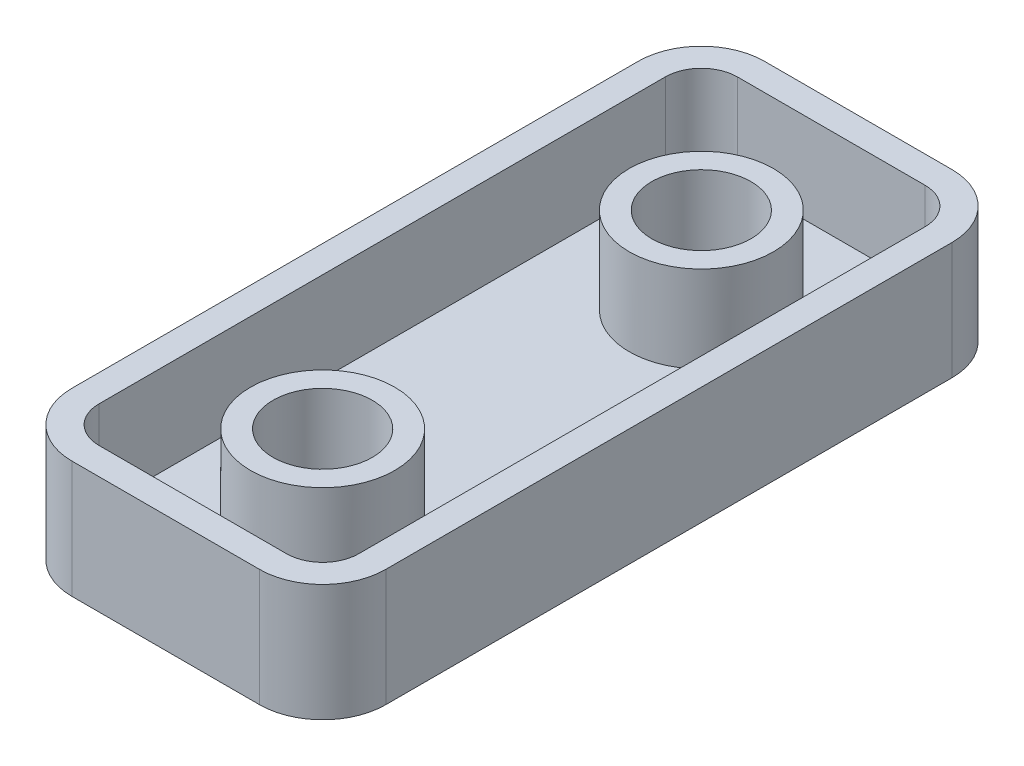
SolidWorks part; units mm, degrees
ref_plane "Front Plane" through (0, 0, 0) normal (0, 0, 1) x (1, 0, 0)
ref_plane "Top Plane" through (0, 0, 0) normal (0, 1, 0) x (1, 0, 0)
ref_plane "Right Plane" through (0, 0, 0) normal (1, 0, 0) x (0, 0, -1)
sketch "Sketch1" plane through (0, 0, 0) normal (0, 1, 0) x (1, 0, 0)
  line L1 (0, 0) -> (-17.4, 0)
  line L2 (0, 0) -> (0, -38.4)
  line L3 (0, -38.4) -> (-17.4, -38.4)
  line L4 (-17.4, 0) -> (-17.4, -38.4)
  dimension "D1" = 17.4
  dimension "D2" = 38.4
  dimension "D3" = 17.4
extrude "Boss-Extrude1" add sketch "Sketch1" along normal blind 6.5
fillet "Fillet1" radius 3.5 4 edges at (-17.4, 3.25, 38.4) (-17.4, 3.25, 0) (0, 3.25, 0) (0, 3.25, 38.4)
sketch "Sketch2" plane through (0, 6.5, 0) normal (0, 1, 0) x (1, 0, 0)
  line L0 (-3.5, 0) -> (-13.9, 0) construction
  line L1 (-13.9, -36.9) -> (-3.5, -36.9)
  line L2 (-15.9, -34.9) -> (-15.9, -3.5)
  line L3 (-13.9, -1.5) -> (-3.5, -1.5)
  line L4 (-1.5, -34.9) -> (-1.5, -3.5)
  line L5 (-15.9, -36.9) -> (-1.5, -1.5) construction
  line L6 (-15.9, -1.5) -> (-1.5, -36.9) construction
  line L7 (-13.9, -38.4) -> (-3.5, -38.4) construction
  line L8 (0, -34.9) -> (0, -3.5) construction
  line L9 (-17.4, -3.5) -> (-17.4, -34.9) construction
  arc A0 (-13.9, -36.9) -> (-15.9, -34.9) centre (-13.9, -34.9) cw
  arc A1 (-3.5, -36.9) -> (-1.5, -34.9) centre (-3.5, -34.9) ccw
  arc A2 (-1.5, -3.5) -> (-3.5, -1.5) centre (-3.5, -3.5) ccw
  arc A3 (-13.9, -1.5) -> (-15.9, -3.5) centre (-13.9, -3.5) ccw
  point P0 (-8.7, -19.2)
  dimension "D5" = 2
  dimension "D1" = 1.5
  dimension "D2" = 1.5
  dimension "D3" = 1.5
  dimension "D4" = 1.5
extrude "Cut-Extrude1" cut sketch "Sketch2" against normal blind 5
sketch "Sketch3" plane through (0, 1.5, 0) normal (0, 1, 0) x (1, 0, 0)
  line L0 (-8.7, -8.7) -> (-8.7, -29.7) construction
  line L1 (-8.7, -1.5) -> (-8.7, -8.7) construction
  line L2 (-3.5, -1.5) -> (-13.9, -1.5) construction
  line L4 (-13.9, -38.4) -> (-3.5, -38.4) construction
  circle A0 centre (-8.7, -29.7) radius 4
  circle A1 centre (-8.7, -29.7) radius 2.75
  circle A2 centre (-8.7, -8.7) radius 4
  circle A3 centre (-8.7, -8.7) radius 2.75
  dimension "D4" = 8
  dimension "D5" = 5.5
  dimension "D1" = 8.7
  dimension "D3" = 21
extrude "Boss-Extrude2" add sketch "Sketch3" along normal blind 4.8
sketch "Sketch4" plane through (0, 1.5, 0) normal (0, 1, 0) x (1, 0, 0)
  circle A0 centre (-8.7, -29.7) radius 2.75 construction
  circle A2 centre (-8.7, -8.7) radius 2.75 construction
  circle A12 centre (-8.7, -29.7) radius 2.75
  circle A14 centre (-8.7, -8.7) radius 2.75
extrude "Cut-Extrude2" cut sketch "Sketch4" against normal blind 0.9
